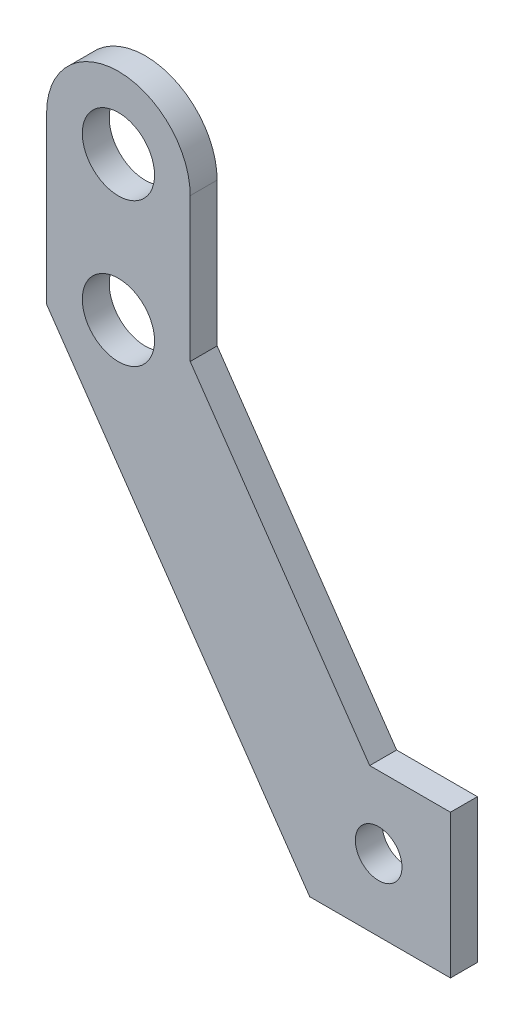
SolidWorks part; units mm, degrees
ref_plane "正面" through (0, 0, 0) normal (0, 0, 1) x (1, 0, 0)
ref_plane "平面" through (0, 0, 0) normal (0, 1, 0) x (1, 0, 0)
ref_plane "右側面" through (0, 0, 0) normal (1, 0, 0) x (0, 0, -1)
sketch "ｽｹｯﾁ1" plane through (0, 0, 0) normal (0, 0, 1) x (1, 0, 0)
  line L3 (0, 46) -> (0, 0) construction
  line L4 (16, 30) -> (16, 46) construction
  line L8 (0, 46) -> (0, 27.5089)
  line L9 (16, 30) -> (16, 46)
  line L10 (0, 27.5089) -> (29.3165, -15) construction
  line L11 (29.3165, -15) -> (45, -15) construction
  line L12 (45, -15) -> (45, 1) construction
  line L13 (45, 1) -> (36, 1) construction
  line L14 (16, 30) -> (36, 1) construction
  line L15 (0, 27.5089) -> (29.3165, -15)
  line L16 (29.3165, -15) -> (45, -15)
  line L17 (45, -15) -> (45, 1)
  line L18 (45, 1) -> (36, 1)
  line L19 (16, 30) -> (36, 1)
  arc A0 (16, 46) -> (0, 46) centre (8, 46) ccw construction
  arc A1 (16, 46) -> (0, 46) centre (8, 46) ccw
  circle A2 centre (8, 46) radius 4 construction
  circle A3 centre (8, 30) radius 4 construction
  circle A4 centre (8, 46) radius 4 construction
  circle A5 centre (8, 30) radius 4 construction
  circle A6 centre (37, -7) radius 2.6
  circle A7 centre (8, 46) radius 4.025
  circle A8 centre (8, 30) radius 4.025
  dimension "D1" = 8
  dimension "D2" = 5.2
  dimension "D4" = 0.025
  dimension "D3" = 8
  dimension "D5" = 0.025
extrude "ﾎﾞｽ - 押し出し1" add sketch "ｽｹｯﾁ1" along normal blind 3
